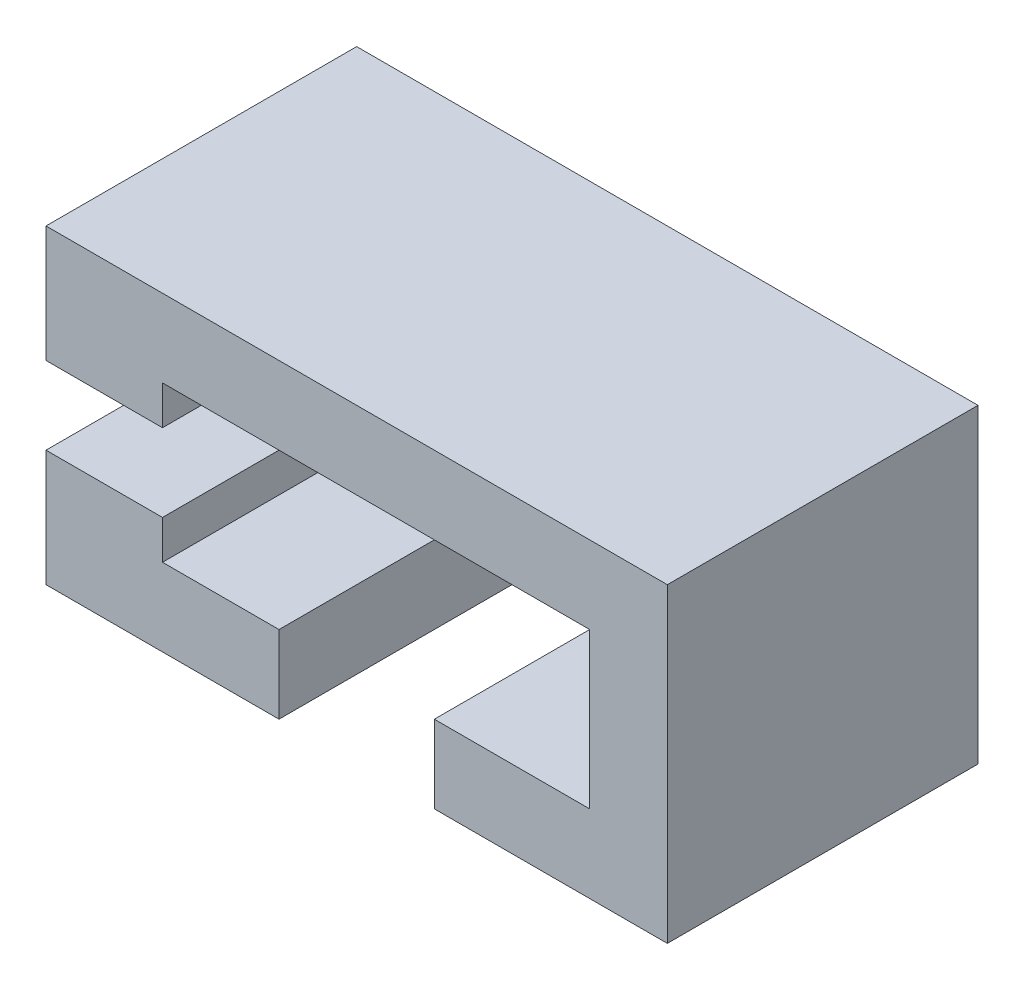
SolidWorks part; units mm, degrees
ref_plane "Front Plane" through (0, 0, 0) normal (0, 0, 1) x (1, 0, 0)
ref_plane "Top Plane" through (0, 0, 0) normal (0, 1, 0) x (1, 0, 0)
ref_plane "Right Plane" through (0, 0, 0) normal (1, 0, 0) x (0, 0, -1)
sketch "Sketch1" plane through (0, 0, 0) normal (1, 0, 0) x (0, 0, -1)
  line L0 (0, 0) -> (0, -15)
  line L1 (0, -15) -> (40, -15)
  line L2 (40, -15) -> (40, 25)
  line L3 (40, 25) -> (0, 25)
  line L4 (0, 25) -> (0, 10)
  line L5 (0, 10) -> (20, 10)
  line L6 (20, 10) -> (20, 0)
  line L7 (20, 0) -> (0, 0)
  dimension "D1" = 40
  dimension "D2" = 10
  dimension "D3" = 20
  dimension "D4" = 40
  dimension "D5" = 15
extrude "Boss-Extrude1" add sketch "Sketch1" against normal blind 80
ref_plane "Plane1" through (0, 0, 0) normal (1, 0, 0) x (0, 0, -1)
sketch "Sketch3" plane through (0, -15, 0) normal (0, -1, 0) x (1, 0, 0)
  line L0 (-30, 0) -> (-30, -40)
  line L1 (-80, 0) -> (0, 0) construction
  line L2 (-80, -40) -> (0, -40) construction
  line L3 (-30, -40) -> (-50, -40)
  line L4 (-50, -40) -> (-50, 0)
  line L5 (-50, 0) -> (-30, 0)
  line L6 (0, -22) -> (0, 22) construction
  dimension "D1" = 20
  dimension "D2" = 30
extrude "Cut-Extrude1" cut sketch "Sketch3" against normal blind 25
sketch "Sketch4" plane through (0, 0, 0) normal (0, 0, 1) x (1, 0, 0)
  line L0 (-65, 10) -> (-65, 15)
  line L1 (-80, 10) -> (0, 10) construction
  line L2 (-65, 15) -> (-10, 15)
  line L3 (-10, 15) -> (-10, 10)
  line L4 (-10, 10) -> (-65, 10)
  line L5 (-80, 25) -> (-80, 10) construction
  dimension "D1" = 15
  dimension "D2" = 70
  dimension "D3" = 5
extrude "Cut-Extrude2" cut sketch "Sketch4" against normal blind 40
sketch "Sketch6" plane through (0, 0, 0) normal (0, 0, 1) x (1, 0, 0)
  line L0 (-30, -5) -> (-10, -5)
  line L1 (-30, -15) -> (-30, 0) construction
  line L2 (-10, -5) -> (-10, 0)
  line L3 (-30, 0) -> (0, 0) construction
  line L4 (-10, 0) -> (-30, 0)
  line L5 (-30, 0) -> (-30, -5)
  dimension "D1" = 5
  dimension "D2" = 20
extrude "Cut-Extrude3" cut sketch "Sketch6" against normal blind 40
sketch "Sketch7" plane through (0, 0, -20) normal (0, 0, 1) x (1, 0, 0)
  line L0 (-10, 0) -> (-10, 10)
  line L1 (-10, 10) -> (-30, 10)
  line L2 (-30, 10) -> (-30, 0)
  line L3 (-30, 0) -> (-10, 0) construction
  line L4 (-30, 0) -> (-30, 10) construction
  line L5 (-30, 0) -> (-10, 0)
extrude "Cut-Extrude4" cut sketch "Sketch7" against normal blind 20
sketch "Sketch8" plane through (0, 0, -20) normal (0, 0, 1) x (1, 0, 0)
  line L0 (0, 0) -> (-10, 0)
  line L1 (-10, 0) -> (-10, 10)
  line L2 (-10, 10) -> (0, 10)
  line L3 (-10, 10) -> (0, 10) construction
  line L4 (0, 10) -> (0, 0)
extrude "Boss-Extrude2" add sketch "Sketch8" along normal blind 20
sketch "Sketch9" plane through (0, 0, -20) normal (0, 0, 1) x (1, 0, 0)
  line L0 (-65, 10) -> (-65, 0)
  line L1 (-80, 0) -> (-50, 0) construction
  line L2 (-65, 0) -> (-50, 0)
  line L3 (-50, 0) -> (-50, 10)
  line L4 (-50, 10) -> (-65, 10)
extrude "Cut-Extrude5" cut sketch "Sketch9" against normal blind 20
sketch "Sketch11" plane through (0, 0, -40) normal (0, 0, -1) x (-1, 0, 0)
  line L0 (50, 0) -> (50, -5)
  line L1 (50, 0) -> (50, -15) construction
  line L2 (50, -5) -> (65, -5)
  line L3 (65, -5) -> (65, 0)
  line L4 (65, 0) -> (50, 0)
  dimension "D1" = 5
extrude "Cut-Extrude6" cut sketch "Sketch11" against normal blind 40
